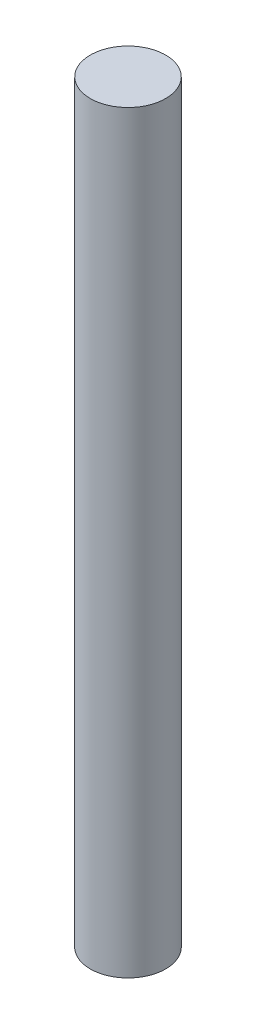
SolidWorks part; units mm, degrees
ref_plane "Front Plane" through (0, 0, 0) normal (0, 0, 1) x (1, 0, 0)
ref_plane "Top Plane" through (0, 0, 0) normal (0, 1, 0) x (1, 0, 0)
ref_plane "Right Plane" through (0, 0, 0) normal (1, 0, 0) x (0, 0, -1)
sketch "Sketch1" plane through (0, 0, 0) normal (0, 1, 0) x (1, 0, 0)
  circle A0 centre (0, 0) radius 1.27
  dimension "D1" = 2.54
extrude "Boss-Extrude1" add sketch "Sketch1" along normal blind 25.4
